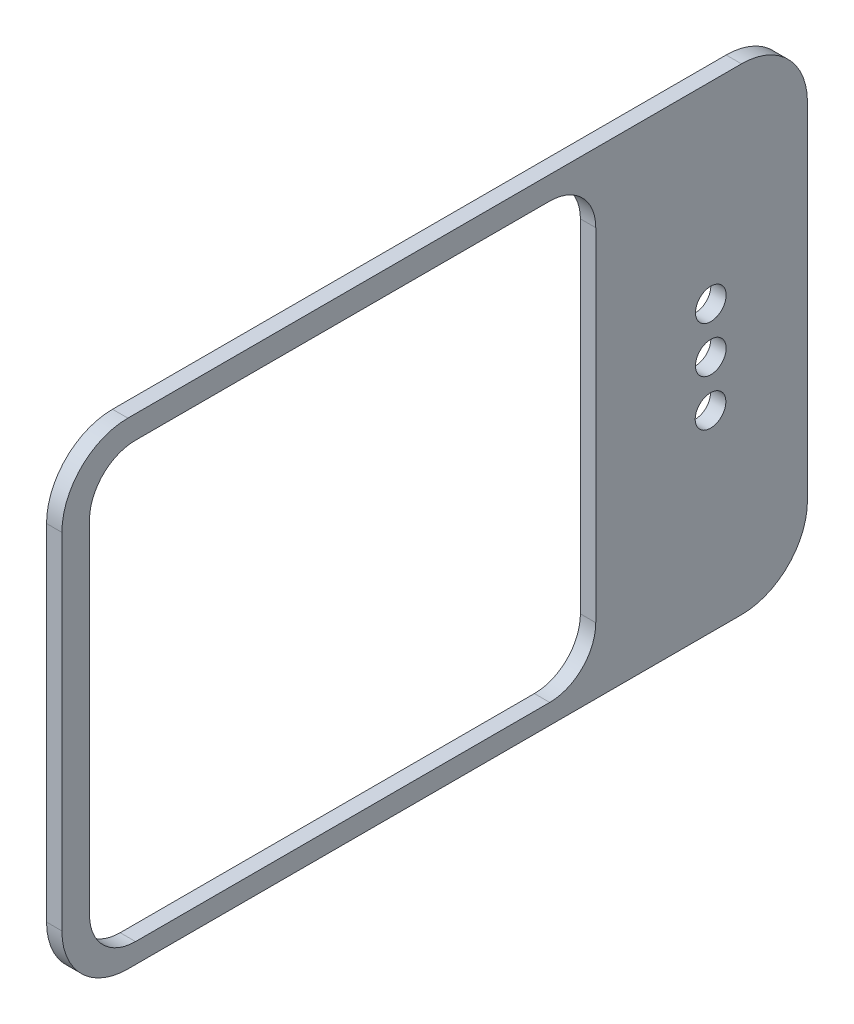
SolidWorks part; units mm, degrees
ref_plane "前视基准面" through (0, 0, 0) normal (0, 0, 1) x (1, 0, 0)
ref_plane "上视基准面" through (0, 0, 0) normal (0, 1, 0) x (1, 0, 0)
ref_plane "右视基准面" through (0, 0, 0) normal (1, 0, 0) x (0, 0, -1)
other "Configuration Table"
sketch "草图1" plane through (0, 0, 0) normal (1, 0, 0) x (0, 0, -1)
  line L16 (26.8098, -1.7475) -> (26.8098, 20.7525)
  line L17 (-17.4902, -6.0475) -> (22.5098, -6.0475)
  line L18 (-21.7902, 20.7525) -> (-21.7902, -1.7475)
  line L19 (22.5098, 25.0525) -> (-17.4902, 25.0525)
  arc A12 (22.5098, -6.0475) -> (26.8098, -1.7475) centre (22.5098, -1.7475) ccw
  arc A13 (-21.7902, -1.7475) -> (-17.4902, -6.0475) centre (-17.4902, -1.7475) ccw
  arc A14 (-17.4902, 25.0525) -> (-21.7902, 20.7525) centre (-17.4902, 20.7525) ccw
  arc A15 (26.8098, 20.7525) -> (22.5098, 25.0525) centre (22.5098, 20.7525) ccw
extrude "凸台-拉伸1" add sketch "草图1" along normal blind 1
sketch "草图2" plane through (0, 0, 0) normal (-1, 0, 0) x (0, 0, 1)
  line L8 (-13.0098, 20.5525) -> (-13.0098, -1.7475)
  line L9 (16.9902, 23.5525) -> (-10.0098, 23.5525)
  line L10 (19.9902, -1.7475) -> (19.9902, 20.5525)
  line L11 (-10.0098, -4.7475) -> (16.9902, -4.7475)
  line L12 (-13.0098, 20.5525) -> (-13.0098, -1.7475)
  line L13 (16.9902, 23.5525) -> (-10.0098, 23.5525)
  line L14 (19.9902, -1.7475) -> (19.9902, 20.5525)
  line L15 (-10.0098, -4.7475) -> (16.9902, -4.7475)
  arc A8 (-10.0098, 23.5525) -> (-13.0098, 20.5525) centre (-10.0098, 20.5525) ccw
  arc A9 (19.9902, 20.5525) -> (16.9902, 23.5525) centre (16.9902, 20.5525) ccw
  arc A10 (16.9902, -4.7475) -> (19.9902, -1.7475) centre (16.9902, -1.7475) ccw
  arc A11 (-13.0098, -1.7475) -> (-10.0098, -4.7475) centre (-10.0098, -1.7475) ccw
  arc A12 (-10.0098, 23.5525) -> (-13.0098, 20.5525) centre (-10.0098, 20.5525) ccw
  arc A13 (19.9902, 20.5525) -> (16.9902, 23.5525) centre (16.9902, 20.5525) ccw
  arc A14 (16.9902, -4.7475) -> (19.9902, -1.7475) centre (16.9902, -1.7475) ccw
  arc A15 (-13.0098, -1.7475) -> (-10.0098, -4.7475) centre (-10.0098, -1.7475) ccw
  dimension "D1" = 0.5
extrude "切除-拉伸1" cut sketch "草图2" against normal through all
sketch "草图3" plane through (0, 0, 0) normal (-1, 0, 0) x (0, 0, 1)
  line L0 (-27.1453, 9.5025) -> (-34.4305, 9.5025) construction
  circle A1 centre (-20.4913, 6.4943) radius 1
  circle A3 centre (-20.5098, 9.5025) radius 1
  circle A4 centre (-20.4913, 6.4943) radius 1
  circle A5 centre (-20.5098, 12.5025) radius 1
  circle A6 centre (-20.5098, 9.5025) radius 1
  circle A7 centre (-20.5098, 12.5025) radius 1
extrude "切除-拉伸2" cut sketch "草图3" against normal through all
